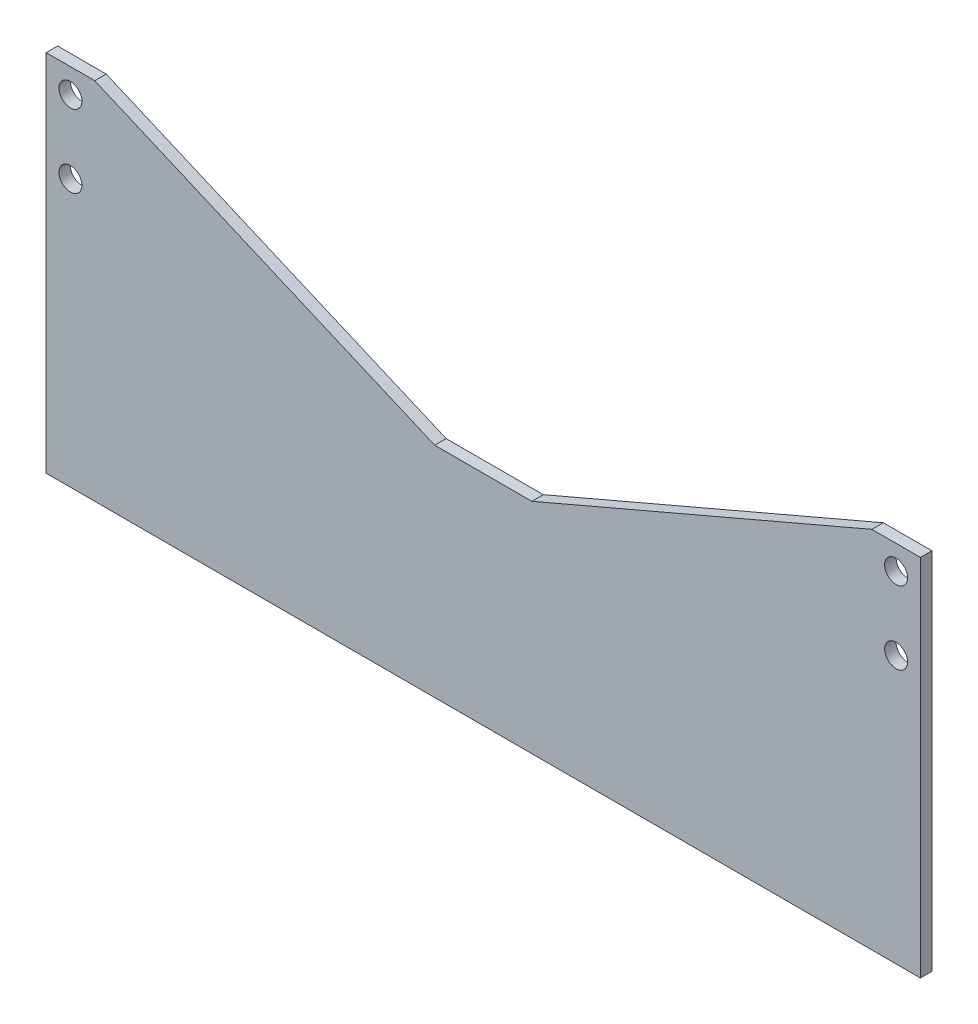
SolidWorks part; units mm, degrees
material "Titanium Ti-5Al-2.5Sn"
ref_plane "Front Plane" through (0, 0, 0) normal (0, 0, 1) x (1, 0, 0)
ref_plane "Top Plane" through (0, 0, 0) normal (0, 1, 0) x (1, 0, 0)
ref_plane "Right Plane" through (0, 0, 0) normal (1, 0, 0) x (0, 0, -1)
sketch "Sketch1" plane through (0, 0, 0) normal (0, 0, 1) x (1, 0, 0)
  line L0 (53.975, 20.6375) -> (57.15, 20.6375) construction
  line L1 (-57.15, -23.8125) -> (57.15, -23.8125)
  line L2 (-57.15, -23.8125) -> (-57.15, 23.8125)
  line L3 (-57.15, 23.8125) -> (-50.8, 23.8125)
  line L4 (57.15, -23.8125) -> (57.15, 23.8125)
  line L5 (-57.15, -23.8125) -> (57.15, 23.8125) construction
  line L6 (-57.15, 23.8125) -> (57.15, -23.8125) construction
  line L7 (-53.975, 20.6375) -> (-57.15, 20.6375) construction
  line L8 (-6.35, 23.8125) -> (6.35, 23.8125) construction
  line L9 (-6.35, 23.8125) -> (6.35, 23.8125) construction
  line L10 (-6.35, 23.8125) -> (-6.35, 4.7625) construction
  line L11 (-6.35, 4.7625) -> (6.35, 4.7625)
  line L12 (6.35, 23.8125) -> (6.35, 4.7625) construction
  line L13 (50.8, 23.8125) -> (57.15, 23.8125)
  line L14 (-6.35, 4.7625) -> (-50.8, 23.8125)
  line L15 (6.35, 4.7625) -> (50.8, 23.8125)
  line L16 (-50.8, 23.8125) -> (-6.35, 23.8125) construction
  line L17 (6.35, 23.8125) -> (50.8, 23.8125) construction
  circle A0 centre (53.975, 20.6375) radius 1.5
  circle A1 centre (53.975, 11.1125) radius 1.5
  circle A2 centre (-53.975, 20.6375) radius 1.5
  circle A3 centre (-53.975, 11.1125) radius 1.5
  point P0 (0, 0)
  point P20 (0, 4.7625)
  dimension "D4" = 3
  dimension "D1" = 47.625
  dimension "D2" = 114.3
  dimension "D3" = 3.175
  dimension "D5" = 3.175
  dimension "D6" = 9.525
  dimension "D7" = 12.7
  dimension "D8" = 19.05
  dimension "D9" = 6.35
extrude "Boss-Extrude1" add sketch "Sketch1" along normal mid plane 1.5
